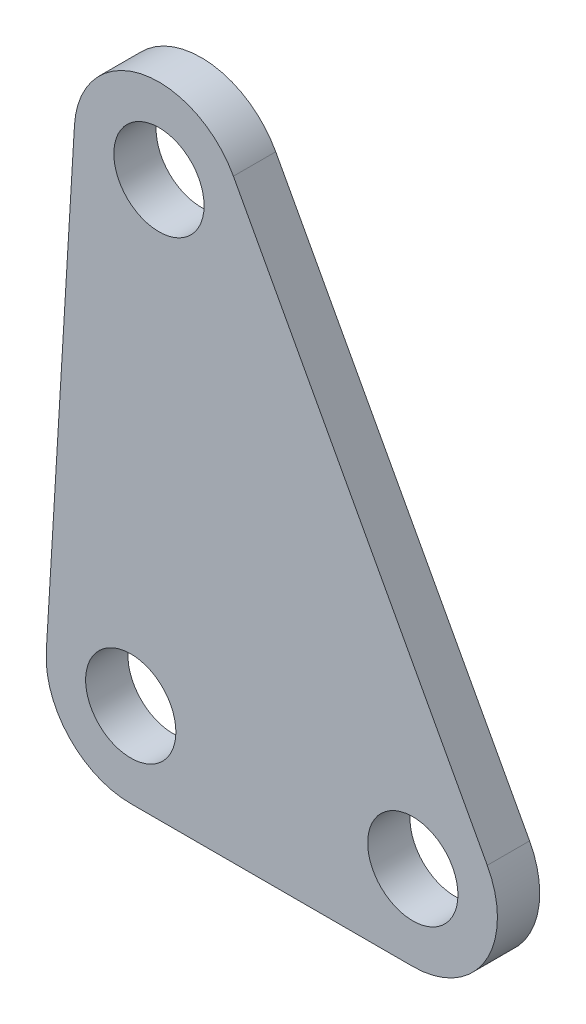
SolidWorks part; units mm, degrees
ref_plane "Front" through (0, 0, 0) normal (0, 0, 1) x (1, 0, 0)
ref_plane "Top" through (0, 0, 0) normal (0, 1, 0) x (1, 0, 0)
ref_plane "Right" through (0, 0, 0) normal (1, 0, 0) x (0, 0, -1)
sketch "Sketch1" plane through (0, 0, 0) normal (0, 0, 1) x (1, 0, 0)
  line L6 (-1, -19.6578) -> (9, -19.6578)
  line L7 (2.6394, 1.426) -> (11.6394, -15.2318)
  line L8 (-2.9946, 0.1798) -> (-3.9946, -16.478)
  circle A0 centre (0, 0) radius 1.6
  arc A11 (2.6394, 1.426) -> (-2.9946, 0.1798) centre (0, 0) ccw
  arc A12 (9, -19.6578) -> (11.6394, -15.2318) centre (9, -16.6578) ccw
  arc A13 (-3.9946, -16.478) -> (-1, -19.6578) centre (-1, -16.6578) ccw
  circle A14 centre (9, -16.6578) radius 1.6
  circle A15 centre (-1, -16.6578) radius 1.6
extrude "Boss-Extrude6" add sketch "Sketch1" along normal blind 1.5
